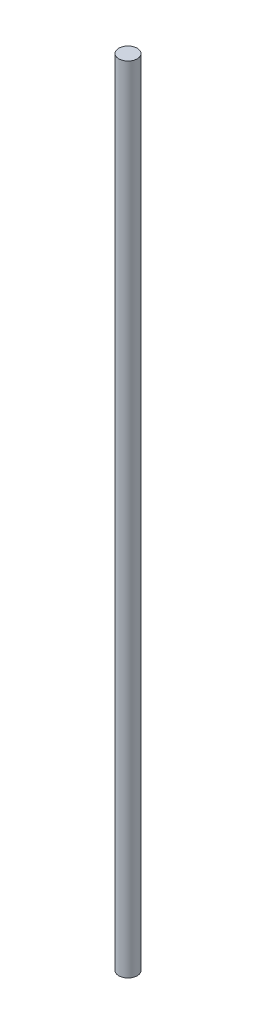
SolidWorks part; units mm, degrees
ref_plane "Front Plane" through (0, 0, 0) normal (0, 0, 1) x (1, 0, 0)
ref_plane "Top Plane" through (0, 0, 0) normal (0, 1, 0) x (1, 0, 0)
ref_plane "Right Plane" through (0, 0, 0) normal (1, 0, 0) x (0, 0, -1)
sketch "Sketch1" plane through (0, 0, 0) normal (0, 1, 0) x (1, 0, 0)
  circle A0 centre (0, 0) radius 4
extrude "Boss-Extrude1" add sketch "Sketch1" along normal blind 345
